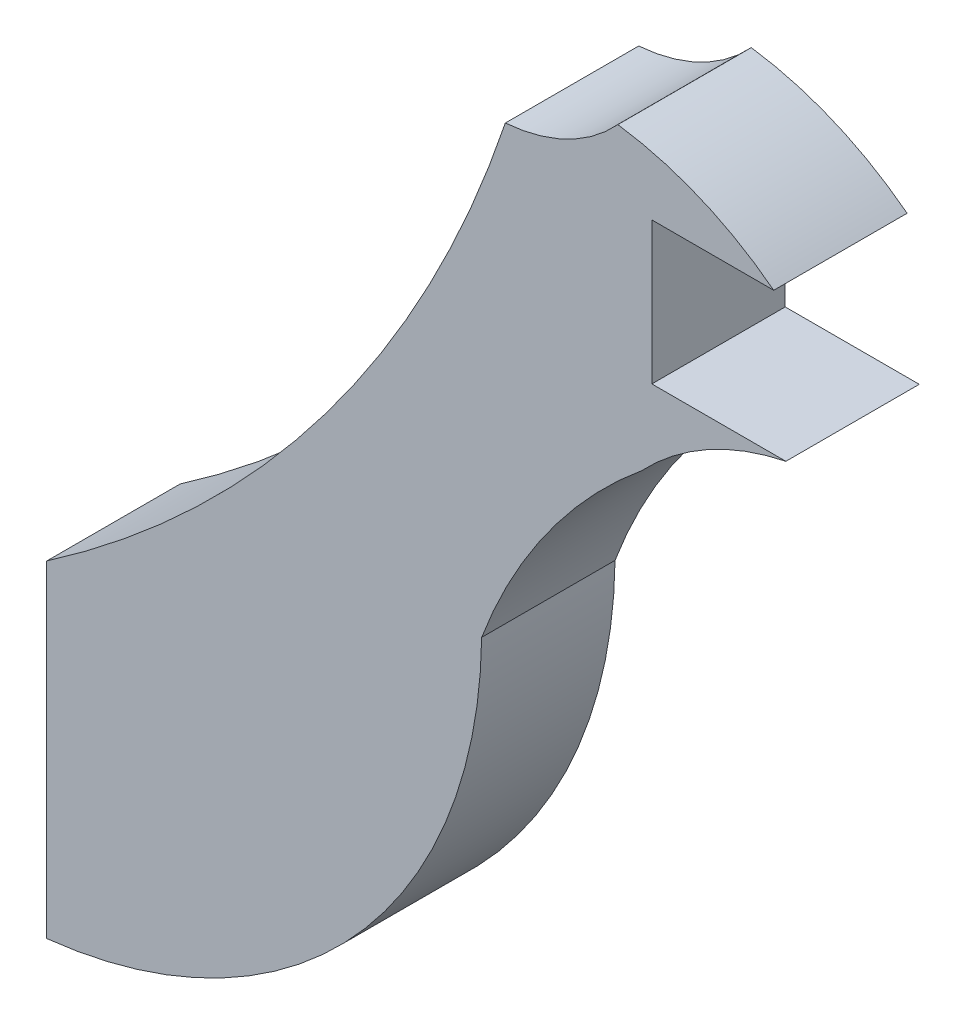
SolidWorks part; units mm, degrees
ref_plane "Front Plane" through (0, 0, 0) normal (0, 0, 1) x (1, 0, 0)
ref_plane "Top Plane" through (0, 0, 0) normal (0, 1, 0) x (1, 0, 0)
ref_plane "Right Plane" through (0, 0, 0) normal (1, 0, 0) x (0, 0, -1)
sketch "Sketch1" plane through (0, 0, 0) normal (0, 0, 1) x (1, 0, 0)
  line L0 (110.8244, -1.524) -> (109.2929, -1.524)
  line L1 (110.8244, -1.524) -> (108.9277, -1.524) construction
  line L2 (109.2929, -1.524) -> (109.2929, 0.0993)
  line L3 (109.2929, 0.0993) -> (110.6857, 0.0993)
  line L5 (102.379, -6.7329) -> (102.379, -10.4692)
  arc A0 (110.6857, 0.0993) -> (108.9048, 0.8481) centre (108.3853, -2.8794) ccw
  arc A1 (108.9048, 0.8481) -> (107.6188, 0.2209) centre (107.4688, 2.1604) cw
  arc A2 (102.379, -10.4692) -> (107.3483, -5.0042) centre (101.7861, -4.9382) ccw
  arc A3 (110.8244, -1.524) -> (109.1782, -2.4388) centre (111.4498, -4.588) ccw
  arc A6 (107.6188, 0.2209) -> (102.379, -6.7329) centre (94.5996, 4.5802) cw
  arc A7 (109.1782, -2.4388) -> (107.3483, -5.0042) centre (113.0489, -7.135) ccw
extrude "Boss-Extrude1" add sketch "Sketch1" along normal blind 1.524
